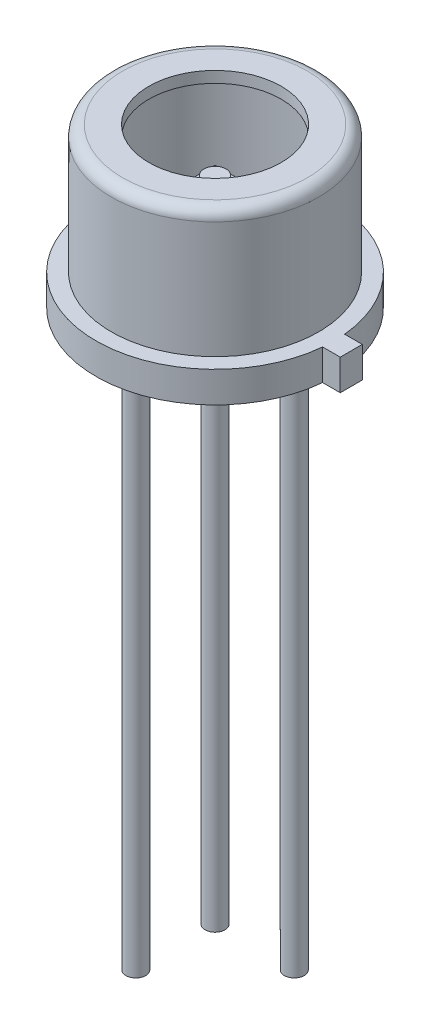
SolidWorks part; units mm, degrees
ref_plane "Front Plane" through (0, 0, 0) normal (0, 0, 1) x (1, 0, 0)
ref_plane "Top Plane" through (0, 0, 0) normal (0, 1, 0) x (1, 0, 0)
ref_plane "Right Plane" through (0, 0, 0) normal (1, 0, 0) x (0, 0, -1)
sketch "Sketch1" plane through (0, 0, 0) normal (0, 0, 1) x (1, 0, 0)
  line L0 (0, 0) -> (0, 37.7864) construction
  line L2 (2.7, 0) -> (2.7, 0.7)
  line L3 (2.7, 0.7) -> (2.35, 0.7)
  line L6 (2.35, 0.7) -> (2.35, 3.346)
  line L7 (2.096, 3.6) -> (1.5, 3.6)
  arc A0 (2.35, 3.346) -> (2.096, 3.6) centre (2.096, 3.346) ccw
  dimension "D7" = 0.254
  dimension "D1" = 0.7
  dimension "D2" = 4.7
  dimension "D4" = 5.4
  dimension "D6" = 3.6
  dimension "D8" = 3
revolve "Revolve-Thin2" add sketch "Sketch1" angle 360 about L0
sketch "Sketch2" plane through (0, 0, 0) normal (0, -1, 0) x (1, 0, 0)
  circle A1 centre (0, 0) radius 2.7
  circle A2 centre (0, 0) radius 2.7
  dimension "D1" = 0
extrude "Boss-Extrude1" add sketch "Sketch2" against normal up to surface (0.446 mm away) up to face at (0, 0.446, -2.096)
sketch "Sketch3" plane through (0, 0, 0) normal (0, -1, 0) x (1, 0, 0)
  line L0 (0.3, 0.3) -> (-0.3, -0.3) construction
  line L1 (-0.3, 0.3) -> (0.3, 0.3)
  line L2 (-0.3, 0.3) -> (-0.3, -0.3)
  line L3 (-0.3, -0.3) -> (0.3, -0.3)
  line L4 (0.3, 0.3) -> (0.3, -0.3)
  dimension "D1" = 0.6
extrude "Boss-Extrude2" add sketch "Sketch3" along normal blind 0.05 from offset 2.5 separate body offset against normal yes
sketch "Sketch8" plane through (0, 2.5, 0) normal (0, 1, 0) x (-1, 0, 0)
  circle A0 centre (0, 0) radius 0.25
  dimension "D1" = 0.5
extrude "Boss-Extrude6" add sketch "Sketch8" along normal blind 0.1 from surface at 0 starting at face at (0, 2.5, 0)
sketch "Sketch11" plane through (0, 0, 0) normal (0, -1, 0) x (1, 0, 0)
  line L0 (0, 0) -> (6.1157, 0) construction
  line L1 (3.0884, 0) -> (3.0884, -0.25)
  line L2 (3.0884, -0.25) -> (2.6884, -0.25)
  line L3 (3.0884, 0) -> (3.0884, 0.25)
  line L4 (3.0884, 0.25) -> (2.6884, 0.25)
  line L5 (0, 0) -> (0, 6.1969) construction
  circle A0 centre (0, 0) radius 4.57
  circle A1 centre (0, 0) radius 2.7 construction
  circle M1 centre (0, 0) radius 2.7
  dimension "D4" = 9.14
  dimension "D1" = 0.5
  dimension "D2" = 0.4
  dimension "D3" = 270
extrude "Boss-Extrude8" add sketch "Sketch11" against normal up to surface (0.7 mm away) contours L3 L4 L2 L1 M1 up to face at (0, 0.7, -2.35)
sketch "Sketch5" plane through (0, 0, 0) normal (0, -1, 0) x (1, 0, 0)
  line L0 (0, 0) -> (-0.898, 0.898) construction
  line L1 (0, 0) -> (1.27, 0) construction
  line L2 (0, 1.6552) -> (0, -1.2761) construction
  circle A0 centre (0, 0) radius 1.27 construction
  circle A2 centre (0.898, -0.898) radius 0.225
  circle A3 centre (-0.898, 0.898) radius 0.225
  circle A4 centre (-0.898, -0.898) radius 0.225
  circle A5 centre (0.898, 0.898) radius 0.225 [skipped]
  dimension "D1" = 2.54
  dimension "D2" = 135
  dimension "D3" = 4
  dimension "D5" = 0.45
extrude "Boss-Extrude4" add sketch "Sketch5" along normal blind 13
sketch "Sketch7" plane through (0, 0, 0) normal (0, -1, 0) x (1, 0, 0)
  circle A0 centre (-0.898, 0.898) radius 0.75
  dimension "D1" = 1.5
extrude "Boss-Extrude5" [suppressed] add sketch "Sketch7" along normal blind 0.4
sketch "Sketch9" plane through (0, 0, 0) normal (0, -1, 0) x (1, 0, 0)
  circle A0 centre (0, -3.8) radius 0.5
  dimension "D1" = 1
  dimension "D2" = 3.8
extrude "Boss-Extrude7" [suppressed] add sketch "Sketch9" along normal blind 0.01
